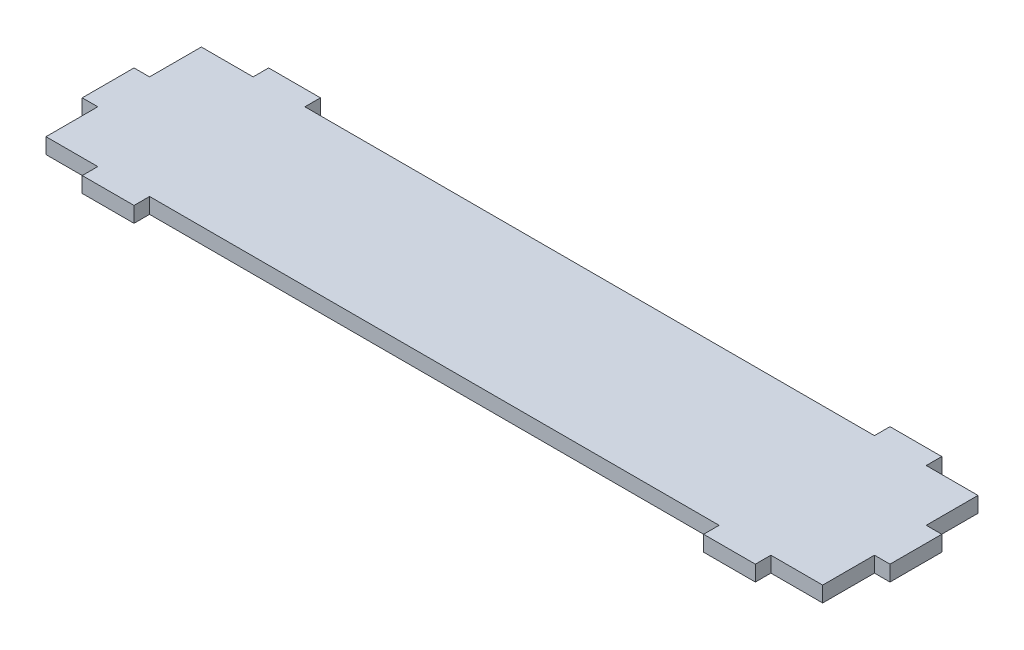
SolidWorks part; units mm, degrees
ref_plane "Plan de face" through (0, 0, 0) normal (0, 0, 1) x (1, 0, 0)
ref_plane "Plan de dessus" through (0, 0, 0) normal (0, 1, 0) x (1, 0, 0)
ref_plane "Plan de droite" through (0, 0, 0) normal (1, 0, 0) x (0, 0, -1)
sketch "Esquisse1" plane through (0, 0, 0) normal (0, 1, 0) x (1, 0, 0)
  line L0 (91.8438, 25.9075) -> (91.8438, 28.9075)
  line L1 (-38.1562, 25.9075) -> (-28.1562, 25.9075)
  line L2 (-38.1562, 25.9075) -> (-38.1562, 15.9075)
  line L3 (-38.1562, -4.0925) -> (-28.1562, -4.0925)
  line L4 (111.8438, 25.9075) -> (111.8438, 15.9075)
  line L6 (-28.1562, 25.9075) -> (-28.1562, 28.9075)
  line L7 (-28.1562, 28.9075) -> (-18.1562, 28.9075)
  line L8 (-18.1562, 25.9075) -> (-18.1562, 28.9075)
  line L9 (-38.1562, 15.9075) -> (-41.1562, 15.9075)
  line L11 (-38.1562, 5.9075) -> (-41.1562, 5.9075)
  line L12 (-41.1562, 15.9075) -> (-41.1562, 5.9075)
  line L14 (101.8438, 25.9075) -> (101.8438, 28.9075)
  line L15 (91.8438, 28.9075) -> (101.8438, 28.9075)
  line L16 (91.8438, -7.0925) -> (91.8438, -4.0925)
  line L17 (91.8438, -7.0925) -> (101.8438, -7.0925)
  line L18 (101.8438, -7.0925) -> (101.8438, -4.0925)
  line L20 (-28.1562, -7.0925) -> (-28.1562, -4.0925)
  line L21 (-28.1562, -7.0925) -> (-18.1562, -7.0925)
  line L22 (-18.1562, -7.0925) -> (-18.1562, -4.0925)
  line L24 (-18.1562, 25.9075) -> (91.8438, 25.9075)
  line L25 (111.8438, 15.9075) -> (114.8438, 15.9075)
  line L27 (111.8438, 5.9075) -> (114.8438, 5.9075)
  line L28 (114.8438, 15.9075) -> (114.8438, 5.9075)
  line L29 (-18.1562, -4.0925) -> (91.8438, -4.0925)
  line L30 (-28.1562, -4.0925) -> (-18.1562, -4.0925) [skipped]
  line L31 (-38.1562, 5.9075) -> (-38.1562, -4.0925)
  line L32 (101.8438, 25.9075) -> (111.8438, 25.9075)
  line L33 (101.8438, -4.0925) -> (111.8438, -4.0925)
  line L34 (91.8438, -4.0925) -> (101.8438, -4.0925) [skipped]
  line L35 (111.8438, 5.9075) -> (111.8438, -4.0925)
  dimension "D1" = 150
  dimension "D2" = 30
  dimension "D3" = 10
  dimension "D4" = 10
  dimension "D5" = 3
  dimension "D6" = 10
  dimension "D7" = 10
  dimension "D8" = 3
  dimension "D11" = 10
  dimension "D12" = 10
  dimension "D13" = 3
  dimension "D9" = 2
  dimension "D10" = 2
extrude "Boss.-Extru.1" add sketch "Esquisse1" along normal blind 3
